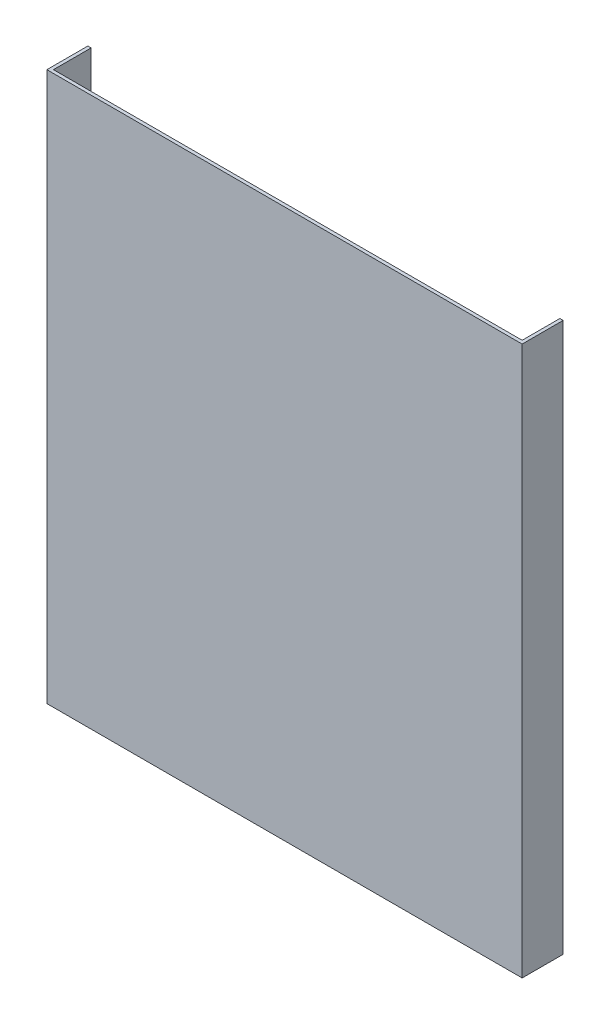
SolidWorks part; units mm, degrees
material "可鍛鑄鐵"
ref_plane "前基準面" through (0, 0, 0) normal (0, 0, 1) x (1, 0, 0)
ref_plane "上基準面" through (0, 0, 0) normal (0, 1, 0) x (1, 0, 0)
ref_plane "右基準面" through (0, 0, 0) normal (1, 0, 0) x (0, 0, -1)
sketch "草圖1" plane through (0, 0, 0) normal (0, 0, 1) x (1, 0, 0)
  line L1 (-113.5905, 61.9585) -> (176.4095, 61.9585)
  line L2 (-113.5905, 61.9585) -> (-113.5905, -273.0415)
  line L3 (-113.5905, -273.0415) -> (176.4095, -273.0415)
  line L4 (176.4095, 61.9585) -> (176.4095, -273.0415)
  dimension "D1" = 290
  dimension "D2" = 335
extrude "填料-伸長1" add sketch "草圖1" along normal blind 2
sketch "草圖2" plane through (0, 0, 0) normal (0, 0, -1) x (-1, 0, 0)
  line L0 (113.5905, -273.0415) -> (-176.4095, -273.0415) construction
  line L1 (113.5905, 61.9585) -> (111.5905, 61.9585)
  line L2 (113.5905, 61.9585) -> (113.5905, -273.0415)
  line L3 (113.5905, -273.0415) -> (111.5905, -273.0415)
  line L4 (111.5905, 61.9585) -> (111.5905, -273.0415)
  line L5 (-176.4095, 61.9585) -> (113.5905, 61.9585) construction
  line L6 (-176.4095, -273.0415) -> (-174.4095, -273.0415)
  line L7 (-176.4095, -273.0415) -> (-176.4095, 61.9585)
  line L8 (-176.4095, 61.9585) -> (-174.4095, 61.9585)
  line L9 (-174.4095, -273.0415) -> (-174.4095, 61.9585)
  dimension "D1" = 2
  dimension "D2" = 2
extrude "填料-伸長2" add sketch "草圖2" along normal blind 23
sketch "草圖3" plane through (0, 0, 2) normal (0, 0, 1) x (1, 0, 0)
  line L0 (-113.5905, 61.9585) -> (-113.5905, -273.0415) construction
  line L1 (-87.5905, 35.9585) -> (-85.5905, 35.9585)
  line L2 (-87.5905, 35.9585) -> (-87.5905, -4.0415)
  line L3 (-87.5905, -4.0415) -> (-85.5905, -4.0415)
  line L4 (-85.5905, 35.9585) -> (-85.5905, -4.0415)
  line L5 (176.4095, 61.9585) -> (-113.5905, 61.9585) construction
  line L6 (176.4095, -273.0415) -> (176.4095, 61.9585) construction
  line L7 (148.4095, 35.9585) -> (150.4095, 35.9585)
  line L8 (148.4095, 35.9585) -> (148.4095, -4.0415)
  line L9 (148.4095, -4.0415) -> (150.4095, -4.0415)
  line L10 (150.4095, 35.9585) -> (150.4095, -4.0415)
  line L12 (-113.5905, -273.0415) -> (176.4095, -273.0415) construction
  line L13 (48.4095, 61.9585) -> (128.4095, 61.9585)
  line L14 (48.4095, 61.9585) -> (48.4095, 59.9585)
  line L15 (48.4095, 59.9585) -> (128.4095, 59.9585)
  line L16 (128.4095, 61.9585) -> (128.4095, 59.9585)
  line L17 (48.4095, -271.0415) -> (128.4095, -271.0415)
  line L18 (48.4095, -271.0415) -> (48.4095, -273.0415)
  line L19 (48.4095, -273.0415) -> (128.4095, -273.0415)
  line L20 (128.4095, -271.0415) -> (128.4095, -273.0415)
  line L22 (-65.5905, 61.9585) -> (-25.5905, 61.9585)
  line L23 (-65.5905, 61.9585) -> (-65.5905, 59.9585)
  line L24 (-65.5905, 59.9585) -> (-25.5905, 59.9585)
  line L25 (-25.5905, 61.9585) -> (-25.5905, 59.9585)
  line L26 (-65.5905, -273.0415) -> (-25.5905, -273.0415)
  line L27 (-65.5905, -273.0415) -> (-65.5905, -271.0415)
  line L28 (-65.5905, -271.0415) -> (-25.5905, -271.0415)
  line L29 (-25.5905, -273.0415) -> (-25.5905, -271.0415)
  dimension "D1" = 28
  dimension "D2" = 2
  dimension "D3" = 40
  dimension "D4" = 26
  dimension "D5" = 40
  dimension "D6" = 2
  dimension "D7" = 26
  dimension "D8" = 28
  dimension "D9" = 80
  dimension "D10" = 2
  dimension "D11" = 20
  dimension "D12" = 2
  dimension "D13" = 80
  dimension "D14" = 2
  dimension "D15" = 20
  dimension "D16" = 2
  dimension "D17" = 2
  dimension "D18" = 40
  dimension "D19" = 40
  dimension "D20" = 2
  dimension "D21" = 2
  dimension "D22" = 20
  dimension "D23" = 20
